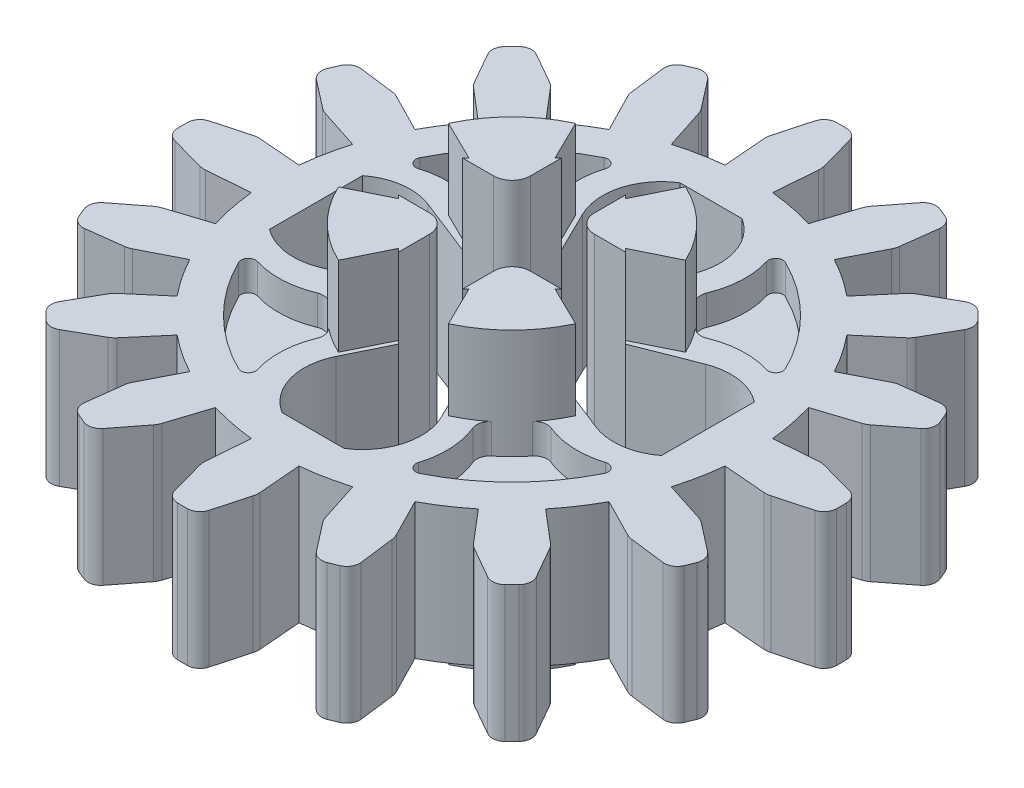
SolidWorks part; units mm, degrees
ref_plane "Front Plane" through (0, 0, 0) normal (0, 0, 1) x (1, 0, 0)
ref_plane "Top Plane" through (0, 0, 0) normal (0, 1, 0) x (1, 0, 0)
ref_plane "Right Plane" through (0, 0, 0) normal (1, 0, 0) x (0, 0, -1)
ref_plane "Plane1" through (0, 1.855, 0) normal (0, 1, 0) x (1, 0, 0)
sketch "Sketch1" plane through (0, 1.855, 0) normal (0, 1, 0) x (1, 0, 0)
  line L0 (-3.7886, 1.4905) -> (-2.2241, 0.875)
  line L1 (-2.2241, 0.875) -> (-0.875, 0.875)
  line L2 (-0.875, 0.875) -> (-0.875, 2.2241)
  line L3 (-0.875, 2.2241) -> (-1.4375, 3.3685)
  line L4 (-0.8471, 5.4344) -> (0.8471, 5.4344)
  line L5 (1.4375, 3.3685) -> (0.875, 2.2241)
  line L6 (0.875, 2.2241) -> (0.875, 0.875)
  line L7 (0.875, 0.875) -> (2.2241, 0.875)
  line L8 (2.2241, 0.875) -> (3.7886, 1.4905)
  line L9 (5.3514, 1.2697) -> (5.3514, -1.2697)
  line L10 (3.7886, -1.4905) -> (2.2241, -0.875)
  line L11 (2.2241, -0.875) -> (0.875, -0.875)
  line L12 (0.875, -0.875) -> (0.875, -2.2241)
  line L13 (0.875, -2.2241) -> (1.4375, -3.3685)
  line L14 (0.8471, -5.4344) -> (-0.8471, -5.4344)
  line L15 (-1.4375, -3.3685) -> (-0.875, -2.2241)
  line L16 (-0.875, -2.2241) -> (-0.875, -0.875)
  line L17 (-0.875, -0.875) -> (-2.2241, -0.875)
  line L18 (-2.2241, -0.875) -> (-3.7886, -1.4905)
  line L19 (-5.3514, -1.2697) -> (-5.3514, 1.2697)
  line L20 (3.0712, 8.4598) -> (2.259, 7.4135)
  line L21 (2.259, 7.4135) -> (1.8745, 6.2239)
  line L22 (0.65, 6.4674) -> (0.75, 7.7136)
  line L23 (0.75, 7.7136) -> (0.4, 8.9911)
  line L24 (-0.4, 8.9911) -> (-0.75, 7.7136)
  line L25 (-0.75, 7.7136) -> (-0.65, 6.4674)
  line L26 (-1.8745, 6.2239) -> (-2.259, 7.4135)
  line L27 (-2.259, 7.4135) -> (-3.0712, 8.4598)
  line L28 (-3.8103, 8.1536) -> (-3.6448, 6.8394)
  line L29 (-3.6448, 6.8394) -> (-3.0755, 5.7264)
  line L30 (-4.1135, 5.0328) -> (-4.924, 5.9847)
  line L31 (-4.924, 5.9847) -> (-6.0748, 6.6405)
  line L32 (-6.6405, 6.0748) -> (-5.9847, 4.924)
  line L33 (-5.9847, 4.924) -> (-5.0328, 4.1135)
  line L34 (-5.7264, 3.0755) -> (-6.8394, 3.6448)
  line L35 (-6.8394, 3.6448) -> (-8.1536, 3.8103)
  line L36 (-8.4598, 3.0712) -> (-7.4135, 2.259)
  line L37 (-7.4135, 2.259) -> (-6.2239, 1.8745)
  line L38 (-6.4674, 0.65) -> (-7.7136, 0.75)
  line L39 (-7.7136, 0.75) -> (-8.9911, 0.4)
  line L40 (-8.9911, -0.4) -> (-7.7136, -0.75)
  line L41 (-7.7136, -0.75) -> (-6.4674, -0.65)
  line L42 (-6.2239, -1.8745) -> (-7.4135, -2.259)
  line L43 (-7.4135, -2.259) -> (-8.4598, -3.0712)
  line L44 (-8.1536, -3.8103) -> (-6.8394, -3.6448)
  line L45 (-6.8394, -3.6448) -> (-5.7264, -3.0755)
  line L46 (-5.0328, -4.1135) -> (-5.9847, -4.924)
  line L47 (-5.9847, -4.924) -> (-6.6405, -6.0748)
  line L48 (-6.0748, -6.6405) -> (-4.924, -5.9847)
  line L49 (-4.924, -5.9847) -> (-4.1135, -5.0328)
  line L50 (-3.0755, -5.7264) -> (-3.6448, -6.8394)
  line L51 (-3.6448, -6.8394) -> (-3.8103, -8.1536)
  line L52 (-3.0712, -8.4598) -> (-2.259, -7.4135)
  line L53 (-2.259, -7.4135) -> (-1.8745, -6.2239)
  line L54 (-0.65, -6.4674) -> (-0.75, -7.7136)
  line L55 (-0.75, -7.7136) -> (-0.4, -8.9911)
  line L56 (0.4, -8.9911) -> (0.75, -7.7136)
  line L57 (0.75, -7.7136) -> (0.65, -6.4674)
  line L58 (1.8745, -6.2239) -> (2.259, -7.4135)
  line L59 (2.259, -7.4135) -> (3.0712, -8.4598)
  line L60 (3.8103, -8.1536) -> (3.6448, -6.8394)
  line L61 (3.6448, -6.8394) -> (3.0755, -5.7264)
  line L62 (4.1135, -5.0328) -> (4.924, -5.9847)
  line L63 (4.924, -5.9847) -> (6.0748, -6.6405)
  line L64 (6.6405, -6.0748) -> (5.9847, -4.924)
  line L65 (5.9847, -4.924) -> (5.0328, -4.1135)
  line L66 (5.7264, -3.0755) -> (6.8394, -3.6448)
  line L67 (6.8394, -3.6448) -> (8.1536, -3.8103)
  line L68 (8.4598, -3.0712) -> (7.4135, -2.259)
  line L69 (7.4135, -2.259) -> (6.2239, -1.8745)
  line L70 (6.4674, -0.65) -> (7.7136, -0.75)
  line L71 (7.7136, -0.75) -> (8.9911, -0.4)
  line L72 (8.9911, 0.4) -> (7.7136, 0.75)
  line L73 (7.7136, 0.75) -> (6.4674, 0.65)
  line L74 (6.2239, 1.8745) -> (7.4135, 2.259)
  line L75 (7.4135, 2.259) -> (8.4598, 3.0712)
  line L76 (8.1536, 3.8103) -> (6.8394, 3.6448)
  line L77 (6.8394, 3.6448) -> (5.7264, 3.0755)
  line L78 (5.0328, 4.1135) -> (5.9847, 4.924)
  line L79 (5.9847, 4.924) -> (6.6405, 6.0748)
  line L80 (6.0748, 6.6405) -> (4.924, 5.9847)
  line L81 (4.924, 5.9847) -> (4.1135, 5.0328)
  line L82 (3.0755, 5.7264) -> (3.6448, 6.8394)
  line L83 (3.6448, 6.8394) -> (3.8103, 8.1536)
  arc A0 (-1.4375, 3.3685) -> (-0.8471, 5.4344) centre (0, 4.075) cw
  arc A1 (0.8471, 5.4344) -> (1.4375, 3.3685) centre (0, 4.075) cw
  arc A2 (3.7886, 1.4905) -> (5.3514, 1.2697) centre (4.375, 0) cw
  arc A3 (5.3514, -1.2697) -> (3.7886, -1.4905) centre (4.375, 0) cw
  arc A4 (1.4375, -3.3685) -> (0.8471, -5.4344) centre (0, -4.075) cw
  arc A5 (-0.8471, -5.4344) -> (-1.4375, -3.3685) centre (0, -4.075) cw
  arc A6 (-3.7886, -1.4905) -> (-5.3514, -1.2697) centre (-4.375, 0) cw
  arc A7 (-5.3514, 1.2697) -> (-3.7886, 1.4905) centre (-4.375, 0) cw
  arc A8 (3.8103, 8.1536) -> (3.0712, 8.4598) centre (0, 0) ccw
  arc A9 (1.8745, 6.2239) -> (0.65, 6.4674) centre (0, 0) ccw
  arc A10 (0.4, 8.9911) -> (-0.4, 8.9911) centre (0, 0) ccw
  arc A11 (-0.65, 6.4674) -> (-1.8745, 6.2239) centre (0, 0) ccw
  arc A12 (-3.0712, 8.4598) -> (-3.8103, 8.1536) centre (0, 0) ccw
  arc A13 (-3.0755, 5.7264) -> (-4.1135, 5.0328) centre (0, 0) ccw
  arc A14 (-6.0748, 6.6405) -> (-6.6405, 6.0748) centre (0, 0) ccw
  arc A15 (-5.0328, 4.1135) -> (-5.7264, 3.0755) centre (0, 0) ccw
  arc A16 (-8.1536, 3.8103) -> (-8.4598, 3.0712) centre (0, 0) ccw
  arc A17 (-6.2239, 1.8745) -> (-6.4674, 0.65) centre (0, 0) ccw
  arc A18 (-8.9911, 0.4) -> (-8.9911, -0.4) centre (0, 0) ccw
  arc A19 (-6.4674, -0.65) -> (-6.2239, -1.8745) centre (0, 0) ccw
  arc A20 (-8.4598, -3.0712) -> (-8.1536, -3.8103) centre (0, 0) ccw
  arc A21 (-5.7264, -3.0755) -> (-5.0328, -4.1135) centre (0, 0) ccw
  arc A22 (-6.6405, -6.0748) -> (-6.0748, -6.6405) centre (0, 0) ccw
  arc A23 (-4.1135, -5.0328) -> (-3.0755, -5.7264) centre (0, 0) ccw
  arc A24 (-3.8103, -8.1536) -> (-3.0712, -8.4598) centre (0, 0) ccw
  arc A25 (-1.8745, -6.2239) -> (-0.65, -6.4674) centre (0, 0) ccw
  arc A26 (-0.4, -8.9911) -> (0.4, -8.9911) centre (0, 0) ccw
  arc A27 (0.65, -6.4674) -> (1.8745, -6.2239) centre (0, 0) ccw
  arc A28 (3.0712, -8.4598) -> (3.8103, -8.1536) centre (0, 0) ccw
  arc A29 (3.0755, -5.7264) -> (4.1135, -5.0328) centre (0, 0) ccw
  arc A30 (6.0748, -6.6405) -> (6.6405, -6.0748) centre (0, 0) ccw
  arc A31 (5.0328, -4.1135) -> (5.7264, -3.0755) centre (0, 0) ccw
  arc A32 (8.1536, -3.8103) -> (8.4598, -3.0712) centre (0, 0) ccw
  arc A33 (6.2239, -1.8745) -> (6.4674, -0.65) centre (0, 0) ccw
  arc A34 (8.9911, -0.4) -> (8.9911, 0.4) centre (0, 0) ccw
  arc A35 (6.4674, 0.65) -> (6.2239, 1.8745) centre (0, 0) ccw
  arc A36 (8.4598, 3.0712) -> (8.1536, 3.8103) centre (0, 0) ccw
  arc A37 (5.7264, 3.0755) -> (5.0328, 4.1135) centre (0, 0) ccw
  arc A38 (6.6405, 6.0748) -> (6.0748, 6.6405) centre (0, 0) ccw
  arc A39 (4.1135, 5.0328) -> (3.0755, 5.7264) centre (0, 0) ccw
extrude "Boss-Extrude1" add sketch "Sketch1" against normal blind 3.71
sketch "Sketch2" plane through (0, -1.855, 0) normal (0, -1, 0) x (1, 0, 0)
  line L0 (-2.2241, -1.0043) -> (-2.2241, -0.875)
  line L1 (-2.2241, -0.875) -> (-0.875, -0.875)
  line L2 (-0.875, -0.875) -> (-0.875, -2.2241)
  line L3 (-0.875, -2.2241) -> (-1.0043, -2.2241)
  line L4 (-1.0043, -2.2241) -> (-1.5021, -3.2369)
  line L5 (-3.2369, -1.5021) -> (-2.2241, -1.0043)
  arc A0 (-1.5021, -3.2369) -> (-3.2369, -1.5021) centre (0, 0) cw
extrude "Boss-Extrude2" add sketch "Sketch2" along normal blind 2.1775
sketch "Sketch3" plane through (0, 1.855, 0) normal (0, 1, 0) x (-1, 0, 0)
  line L0 (2.2241, -0.875) -> (2.2241, -1.0043)
  line L1 (2.2241, -1.0043) -> (3.2369, -1.5021)
  line L2 (1.5021, -3.2369) -> (1.0043, -2.2241)
  line L3 (1.0043, -2.2241) -> (0.875, -2.2241)
  line L4 (0.875, -2.2241) -> (0.875, -0.875)
  line L5 (0.875, -0.875) -> (2.2241, -0.875)
  arc A0 (3.2369, -1.5021) -> (1.5021, -3.2369) centre (0, 0) cw
extrude "Boss-Extrude3" add sketch "Sketch3" along normal blind 2.1775
sketch "Sketch4" plane through (0, -1.855, 0) normal (0, -1, 0) x (1, 0, 0)
  line L0 (-1.0043, 2.2241) -> (-0.875, 2.2241)
  line L1 (-0.875, 2.2241) -> (-0.875, 0.875)
  line L2 (-0.875, 0.875) -> (-2.2241, 0.875)
  line L3 (-2.2241, 0.875) -> (-2.2241, 1.0043)
  line L4 (-2.2241, 1.0043) -> (-3.2369, 1.5021)
  line L5 (-1.5021, 3.2369) -> (-1.0043, 2.2241)
  arc A0 (-3.2369, 1.5021) -> (-1.5021, 3.2369) centre (0, 0) cw
extrude "Boss-Extrude4" add sketch "Sketch4" along normal blind 2.1775
sketch "Sketch5" plane through (0, 1.855, 0) normal (0, 1, 0) x (-1, 0, 0)
  line L0 (0.875, 2.2241) -> (1.0043, 2.2241)
  line L1 (1.0043, 2.2241) -> (1.5021, 3.2369)
  line L2 (3.2369, 1.5021) -> (2.2241, 1.0043)
  line L3 (2.2241, 1.0043) -> (2.2241, 0.875)
  line L4 (2.2241, 0.875) -> (0.875, 0.875)
  line L5 (0.875, 0.875) -> (0.875, 2.2241)
  arc A0 (1.5021, 3.2369) -> (3.2369, 1.5021) centre (0, 0) cw
extrude "Boss-Extrude5" add sketch "Sketch5" along normal blind 2.1775
sketch "Sketch6" plane through (0, -1.855, 0) normal (0, -1, 0) x (1, 0, 0)
  line L0 (2.2241, 1.0043) -> (2.2241, 0.875)
  line L1 (2.2241, 0.875) -> (0.875, 0.875)
  line L2 (0.875, 0.875) -> (0.875, 2.2241)
  line L3 (0.875, 2.2241) -> (1.0043, 2.2241)
  line L4 (1.0043, 2.2241) -> (1.5021, 3.2369)
  line L5 (3.2369, 1.5021) -> (2.2241, 1.0043)
  arc A0 (1.5021, 3.2369) -> (3.2369, 1.5021) centre (0, 0) cw
extrude "Boss-Extrude6" add sketch "Sketch6" along normal blind 2.1775
sketch "Sketch7" plane through (0, 1.855, 0) normal (0, 1, 0) x (-1, 0, 0)
  line L0 (-2.2241, 0.875) -> (-2.2241, 1.0043)
  line L1 (-2.2241, 1.0043) -> (-3.2369, 1.5021)
  line L2 (-1.5021, 3.2369) -> (-1.0043, 2.2241)
  line L3 (-1.0043, 2.2241) -> (-0.875, 2.2241)
  line L4 (-0.875, 2.2241) -> (-0.875, 0.875)
  line L5 (-0.875, 0.875) -> (-2.2241, 0.875)
  arc A0 (-3.2369, 1.5021) -> (-1.5021, 3.2369) centre (0, 0) cw
extrude "Boss-Extrude7" add sketch "Sketch7" along normal blind 2.1775
sketch "Sketch8" plane through (0, 1.855, 0) normal (0, 1, 0) x (-1, 0, 0)
  line L0 (-0.875, -2.2241) -> (-1.0043, -2.2241)
  line L1 (-1.0043, -2.2241) -> (-1.5021, -3.2369)
  line L2 (-3.2369, -1.5021) -> (-2.2241, -1.0043)
  line L3 (-2.2241, -1.0043) -> (-2.2241, -0.875)
  line L4 (-2.2241, -0.875) -> (-0.875, -0.875)
  line L5 (-0.875, -0.875) -> (-0.875, -2.2241)
  arc A0 (-1.5021, -3.2369) -> (-3.2369, -1.5021) centre (0, 0) cw
extrude "Boss-Extrude8" add sketch "Sketch8" along normal blind 2.1775
sketch "Sketch9" plane through (0, -1.855, 0) normal (0, -1, 0) x (1, 0, 0)
  line L0 (1.0043, -2.2241) -> (0.875, -2.2241)
  line L1 (0.875, -2.2241) -> (0.875, -0.875)
  line L2 (0.875, -0.875) -> (2.2241, -0.875)
  line L3 (2.2241, -0.875) -> (2.2241, -1.0043)
  line L4 (2.2241, -1.0043) -> (3.2369, -1.5021)
  line L5 (1.5021, -3.2369) -> (1.0043, -2.2241)
  arc A0 (3.2369, -1.5021) -> (1.5021, -3.2369) centre (0, 0) cw
extrude "Boss-Extrude9" add sketch "Sketch9" along normal blind 2.1775
sketch "Sketch10" plane through (0, 1.855, 0) normal (0, 1, 0) x (-1, 0, 0)
  arc A0 (2.9508, 2.0066) -> (4.7537, 2.1976) centre (4.075, 0) cw
  arc A1 (4.7537, 2.1976) -> (4.9919, 2.4776) centre (4.8128, 2.3887) ccw
  arc A2 (4.9919, 2.4776) -> (2.4776, 4.9919) centre (0, 0) ccw
  arc A3 (2.4776, 4.9919) -> (2.1976, 4.7537) centre (2.3887, 4.8128) ccw
  arc A4 (2.1976, 4.7537) -> (2.0066, 2.9508) centre (0, 4.075) cw
  arc A5 (2.0066, 2.9508) -> (2.9508, 2.0066) centre (0, 0) cw
extrude "Cut-Extrude1" cut sketch "Sketch10" against normal blind 0.815
sketch "Sketch11" plane through (0, 1.855, 0) normal (0, 1, 0) x (-1, 0, 0)
  arc A0 (2.0066, -2.9508) -> (2.1976, -4.7537) centre (0, -4.075) cw
  arc A1 (2.1976, -4.7537) -> (2.4776, -4.9919) centre (2.3887, -4.8128) ccw
  arc A2 (2.4776, -4.9919) -> (4.9919, -2.4776) centre (0, 0) ccw
  arc A3 (4.9919, -2.4776) -> (4.7537, -2.1976) centre (4.8128, -2.3887) ccw
  arc A4 (4.7537, -2.1976) -> (2.9508, -2.0066) centre (4.075, 0) cw
  arc A5 (2.9508, -2.0066) -> (2.0066, -2.9508) centre (0, 0) cw
extrude "Cut-Extrude2" cut sketch "Sketch11" against normal blind 0.815
sketch "Sketch12" plane through (0, 1.855, 0) normal (0, 1, 0) x (-1, 0, 0)
  arc A0 (-2.9508, -2.0066) -> (-4.7537, -2.1976) centre (-4.075, 0) cw
  arc A1 (-4.7537, -2.1976) -> (-4.9919, -2.4776) centre (-4.8128, -2.3887) ccw
  arc A2 (-4.9919, -2.4776) -> (-2.4776, -4.9919) centre (0, 0) ccw
  arc A3 (-2.4776, -4.9919) -> (-2.1976, -4.7537) centre (-2.3887, -4.8128) ccw
  arc A4 (-2.1976, -4.7537) -> (-2.0066, -2.9508) centre (0, -4.075) cw
  arc A5 (-2.0066, -2.9508) -> (-2.9508, -2.0066) centre (0, 0) cw
extrude "Cut-Extrude3" cut sketch "Sketch12" against normal blind 0.815
sketch "Sketch13" plane through (0, -1.855, 0) normal (0, -1, 0) x (1, 0, 0)
  arc A0 (4.7537, -2.1976) -> (2.9508, -2.0066) centre (4.075, 0) cw
  arc A1 (2.9508, -2.0066) -> (2.0066, -2.9508) centre (0, 0) cw
  arc A2 (2.0066, -2.9508) -> (2.1976, -4.7537) centre (0, -4.075) cw
  arc A3 (2.1976, -4.7537) -> (2.4776, -4.9919) centre (2.3887, -4.8128) ccw
  arc A4 (2.4776, -4.9919) -> (4.9919, -2.4776) centre (0, 0) ccw
  arc A5 (4.9919, -2.4776) -> (4.7537, -2.1976) centre (4.8128, -2.3887) ccw
extrude "Cut-Extrude4" cut sketch "Sketch13" against normal blind 0.815
sketch "Sketch14" plane through (0, -1.855, 0) normal (0, -1, 0) x (1, 0, 0)
  arc A0 (-4.7537, 2.1976) -> (-2.9508, 2.0066) centre (-4.075, 0) cw
  arc A1 (-2.9508, 2.0066) -> (-2.0066, 2.9508) centre (0, 0) cw
  arc A2 (-2.0066, 2.9508) -> (-2.1976, 4.7537) centre (0, 4.075) cw
  arc A3 (-2.1976, 4.7537) -> (-2.4776, 4.9919) centre (-2.3887, 4.8128) ccw
  arc A4 (-2.4776, 4.9919) -> (-4.9919, 2.4776) centre (0, 0) ccw
  arc A5 (-4.9919, 2.4776) -> (-4.7537, 2.1976) centre (-4.8128, 2.3887) ccw
extrude "Cut-Extrude5" cut sketch "Sketch14" against normal blind 0.815
sketch "Sketch15" plane through (0, -1.855, 0) normal (0, -1, 0) x (1, 0, 0)
  arc A0 (-2.1976, -4.7537) -> (-2.0066, -2.9508) centre (0, -4.075) cw
  arc A1 (-2.0066, -2.9508) -> (-2.9508, -2.0066) centre (0, 0) cw
  arc A2 (-2.9508, -2.0066) -> (-4.7537, -2.1976) centre (-4.075, 0) cw
  arc A3 (-4.7537, -2.1976) -> (-4.9919, -2.4776) centre (-4.8128, -2.3887) ccw
  arc A4 (-4.9919, -2.4776) -> (-2.4776, -4.9919) centre (0, 0) ccw
  arc A5 (-2.4776, -4.9919) -> (-2.1976, -4.7537) centre (-2.3887, -4.8128) ccw
extrude "Cut-Extrude6" cut sketch "Sketch15" against normal blind 0.815
sketch "Sketch16" plane through (0, -1.855, 0) normal (0, -1, 0) x (1, 0, 0)
  arc A0 (2.1976, 4.7537) -> (2.0066, 2.9508) centre (0, 4.075) cw
  arc A1 (2.0066, 2.9508) -> (2.9508, 2.0066) centre (0, 0) cw
  arc A2 (2.9508, 2.0066) -> (4.7537, 2.1976) centre (4.075, 0) cw
  arc A3 (4.7537, 2.1976) -> (4.9919, 2.4776) centre (4.8128, 2.3887) ccw
  arc A4 (4.9919, 2.4776) -> (2.4776, 4.9919) centre (0, 0) ccw
  arc A5 (2.4776, 4.9919) -> (2.1976, 4.7537) centre (2.3887, 4.8128) ccw
extrude "Cut-Extrude7" cut sketch "Sketch16" against normal blind 0.815
sketch "Sketch17" plane through (0, 1.855, 0) normal (0, 1, 0) x (-1, 0, 0)
  arc A0 (-2.0066, 2.9508) -> (-2.1976, 4.7537) centre (0, 4.075) cw
  arc A1 (-2.1976, 4.7537) -> (-2.4776, 4.9919) centre (-2.3887, 4.8128) ccw
  arc A2 (-2.4776, 4.9919) -> (-4.9919, 2.4776) centre (0, 0) ccw
  arc A3 (-4.9919, 2.4776) -> (-4.7537, 2.1976) centre (-4.8128, 2.3887) ccw
  arc A4 (-4.7537, 2.1976) -> (-2.9508, 2.0066) centre (-4.075, 0) cw
  arc A5 (-2.9508, 2.0066) -> (-2.0066, 2.9508) centre (0, 0) cw
extrude "Cut-Extrude8" cut sketch "Sketch17" against normal blind 0.815
draft "Draft1" type of draft neutral plane draft angle 44.305 faces to draft 2 face at (0.9397, 2.9438, 2.2241) face at (0.9397, -2.9437, 2.2241) neutral plane through (0.875, -1.855, 0.875) neutral plane normal (-1, 0, 0) reverse direction yes parameters "D1"=44.305
draft "Draft2" type of draft neutral plane draft angle 44.305 faces to draft 2 face at (2.2241, -2.9437, 0.9397) face at (2.2241, 2.9438, 0.9397) neutral plane through (2.2241, -1.855, 0.875) neutral plane normal (0, 0, -1) reverse direction yes parameters "D1"=44.305
draft "Draft3" type of draft neutral plane draft angle 44.305 faces to draft 2 face at (0.9397, -2.9437, -2.2241) face at (0.9397, 2.9438, -2.2241) neutral plane through (0.875, -1.855, -2.2241) neutral plane normal (-1, 0, 0) reverse direction yes parameters "D1"=44.305
draft "Draft4" type of draft neutral plane draft angle 44.305 faces to draft 2 face at (2.2241, 2.9438, -0.9397) face at (2.2241, -2.9437, -0.9397) neutral plane through (0.875, -1.855, -0.875) neutral plane normal (0, 0, 1) reverse direction yes parameters "D1"=44.305
draft "Draft5" type of draft neutral plane draft angle 44.305 faces to draft 2 face at (-0.9397, 2.9438, -2.2241) face at (-0.9397, -2.9437, -2.2241) neutral plane through (-0.875, -1.855, -0.875) neutral plane normal (1, 0, 0) reverse direction yes parameters "D1"=44.305
draft "Draft6" type of draft neutral plane draft angle 44.305 faces to draft 2 face at (-2.2241, -2.9437, -0.9397) face at (-2.2241, 2.9438, -0.9397) neutral plane through (-2.2241, -1.855, -0.875) neutral plane normal (0, 0, 1) reverse direction yes parameters "D1"=44.305
draft "Draft7" type of draft neutral plane draft angle 44.305 faces to draft 2 face at (-0.9397, -2.9437, 2.2241) face at (-0.9397, 2.9438, 2.2241) neutral plane through (-0.875, -1.855, 2.2241) neutral plane normal (1, 0, 0) reverse direction yes parameters "D1"=44.305
draft "Draft8" type of draft neutral plane draft angle 44.305 faces to draft 2 face at (-2.2241, 2.9438, 0.9397) face at (-2.2241, -2.9437, 0.9397) neutral plane through (-0.875, -1.855, 0.875) neutral plane normal (0, 0, -1) reverse direction yes parameters "D1"=44.305
fillet "Fillet1" radius 0.35 48 edges at (3.0712, 0, -8.4598) (-2.0066, 1.4475, 2.9508) (-2.0066, -1.4475, 2.9508) (2.9508, -1.4475, 2.0066) (2.0066, 1.4475, -2.9508) (6.6405, 0, 6.0748) (8.9911, 0, -0.4) (8.1536, 0, -3.8103) (-6.0748, 0, -6.6405) (-3.8103, 0, -8.1536) (-2.9508, 1.4475, -2.0066) (-8.9911, 0, 0.4) (2.9508, 1.4475, 2.0066) (-3.0712, 0, -8.4598) (8.9911, 0, 0.4) (3.0712, 0, 8.4598) (-6.6405, 0, -6.0748) (-8.9911, 0, -0.4) (-2.9508, -1.4475, -2.0066) (6.6405, 0, -6.0748) (2.0066, -1.4475, -2.9508) (-6.0748, 0, 6.6405) (-2.9508, 1.4475, 2.0066) (6.0748, 0, -6.6405) (-2.0066, 1.4475, -2.9508) (-0.4, 0, -8.9911) (2.9508, 1.4475, -2.0066) (3.8103, 0, 8.1536) (-8.4598, 0, 3.0712) (0.4, 0, -8.9911) (-6.6405, 0, 6.0748) (8.1536, 0, 3.8103) (-3.8103, 0, 8.1536) (-8.1536, 0, 3.8103) (2.0066, -1.4475, 2.9508) (3.8103, 0, -8.1536) (6.0748, 0, 6.6405) (8.4598, 0, 3.0712) (-2.9508, -1.4475, 2.0066) (-8.4598, 0, -3.0712) (-2.0066, -1.4475, -2.9508) (-0.4, 0, 8.9911) (0.4, 0, 8.9911) (-8.1536, 0, -3.8103) (2.9508, -1.4475, -2.0066) (2.0066, 1.4475, 2.9508) (-3.0712, 0, 8.4598) (8.4598, 0, -3.0712)
fillet "Fillet2" radius 0.5 36 edges at (-5.9847, 0, 4.924) (0.875, 0, 0.875) (-0.75, 0, -7.7136) (3.6448, 0, 6.8394) (2.259, 0, -7.4135) (-7.4135, 0, 2.259) (-2.259, 0, -7.4135) (4.924, 0, 5.9847) (0.75, 0, -7.7136) (-7.7136, 0, 0.75) (-0.875, 0, -0.875) (5.9847, 0, 4.924) (-4.924, 0, 5.9847) (-7.7136, 0, -0.75) (-6.8394, 0, 3.6448) (6.8394, 0, 3.6448) (5.9847, 0, -4.924) (-7.4135, 0, -2.259) (4.924, 0, -5.9847) (7.4135, 0, 2.259) (3.6448, 0, -6.8394) (-6.8394, 0, -3.6448) (-0.875, 0, 0.875) (7.7136, 0, 0.75) (0.875, 0, -0.875) (-2.259, 0, 7.4135) (-0.75, 0, 7.7136) (-3.6448, 0, 6.8394) (0.75, 0, 7.7136) (-4.924, 0, -5.9847) (2.259, 0, 7.4135) (-3.6448, 0, -6.8394) (6.8394, 0, -3.6448) (-5.9847, 0, -4.924) (7.7136, 0, -0.75) (7.4135, 0, -2.259)
